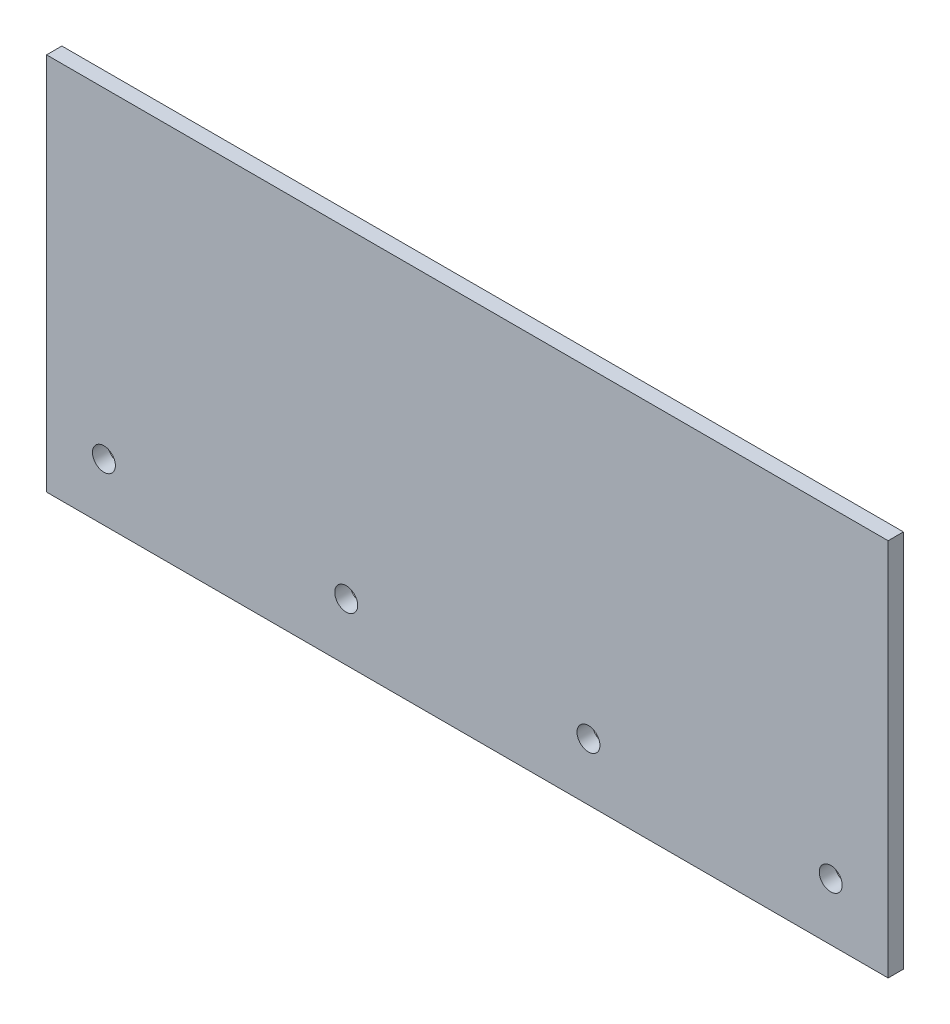
SolidWorks part; units mm, degrees
ref_plane "Přední rovina" through (0, 0, 0) normal (0, 0, 1) x (1, 0, 0)
ref_plane "Horní rovina" through (0, 0, 0) normal (0, 1, 0) x (1, 0, 0)
ref_plane "Pravá rovina" through (0, 0, 0) normal (1, 0, 0) x (0, 0, -1)
sketch "Skica1" plane through (0, 0, 0) normal (0, 0, 1) x (1, 0, 0)
  line L0 (220, 15) -> (0, 15) construction
  line L3 (0, 99) -> (220, 99)
  line L5 (0, 0) -> (220, 0)
  line L6 (0, 99) -> (0, 0)
  line L8 (220, 0) -> (220, 99)
  line L11 (110, 99) -> (110, -101) construction
  circle A0 centre (205, 15) radius 3
  circle A1 centre (15, 15) radius 3
  circle A2 centre (141.6667, 15) radius 3
  circle A3 centre (78.3333, 15) radius 3
extrude "Přidat vysunutím1" add sketch "Skica1" along normal blind 4
equation "\"D8@Skica1\"=\"D7@Skica1\"/3"
equation "\"D9@Skica1\"=\"D8@Skica1\""
